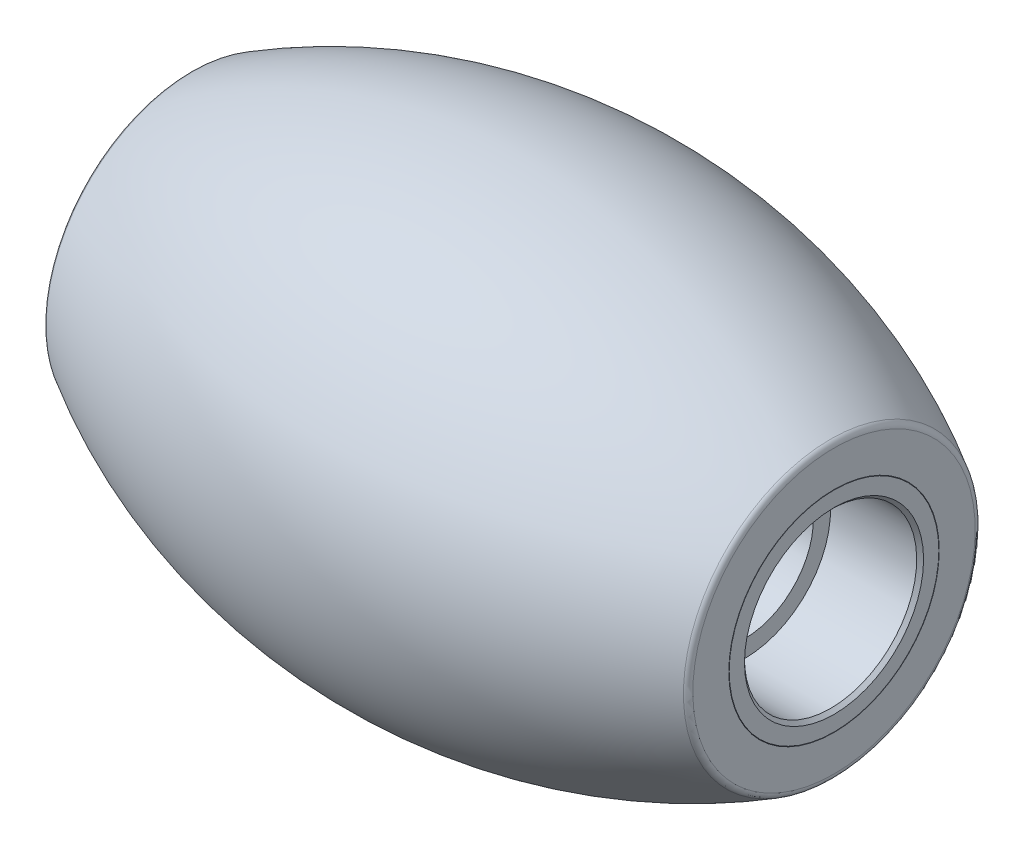
SolidWorks part; units mm, degrees
ref_plane "Face" through (0, 0, 0) normal (0, 0, 1) x (1, 0, 0)
ref_plane "Dessus" through (0, 0, 0) normal (0, 1, 0) x (1, 0, 0)
ref_plane "Droite" through (0, 0, 0) normal (1, 0, 0) x (0, 0, -1)
sketch "Esquisse1" plane through (0, 0, 0) normal (0, 0, 1) x (1, 0, 0)
  line L0 (-9.35, 0) -> (9.35, 0) construction
  line L1 (9.35, 0) -> (9.35, 3.0428)
  line L2 (-9.35, 3.0428) -> (-9.35, 0)
  line L3 (0, 0) -> (0, 5.75) construction
  line L4 (-9.35, 0) -> (9.35, 0)
  arc A0 (-9.35, 3.0428) -> (9.35, 3.0428) centre (0, -11.75) cw
  dimension "D1" = 11.5
  dimension "D3" = 17.5
  dimension "D2" = 18.7
revolve "Révolution1" add sketch "Esquisse1" angle 360 about L4
sketch "Esquisse2" plane through (0, 0, 0) normal (0, 0, 1) x (1, 0, 0)
  line L0 (-9.35, 2.5) -> (-6.75, 2.5)
  line L1 (-9.35, 3.0428) -> (-9.35, -3.0428) construction
  line L2 (-6.75, 2.5) -> (-6.75, 2)
  line L3 (-6.75, 2) -> (6.75, 2)
  line L4 (6.75, 2) -> (6.75, 2.5)
  line L5 (6.75, 2.5) -> (9.35, 2.5)
  line L6 (9.35, -3.0428) -> (9.35, 3.0428) construction
  line L7 (-9.35, 0) -> (9.35, 0) construction
  line L8 (-9.35, 2.5) -> (-9.35, 0)
  line L9 (9.35, 2.5) -> (9.35, 0)
  line L10 (-9.35, 0) -> (9.35, 0)
  dimension "D1" = 5
  dimension "D2" = 2.6
  dimension "D3" = 4
revolve "Enlèvement de matière-Révolution1" cut sketch "Esquisse2" angle 360 about L7
chamfer "Chanfrein1" distance 0.1 angle 45 2 edges at (-9.35, -2.5, 0) (9.35, -2.5, 0)
sketch "Esquisse4" plane through (0, 0, 0) normal (0, 0, 1) x (1, 0, 0)
  line L0 (-9.35, 3.0546) -> (-9.35, 4.2133)
  line L1 (9.35, 3.0546) -> (9.35, 4.2133)
  line L2 (-9.35, 0) -> (9.35, 0) construction
  line L3 (-9.35, 2.6) -> (-9.35, -2.6) construction
  line L4 (9.35, -2.6) -> (9.35, 2.6) construction
  arc A0 (9.35, 3.0428) -> (-9.35, 3.0428) centre (0, -11.75) ccw
  arc A1 (-9.35, -3.0428) -> (9.35, -3.0428) centre (0, 11.75) ccw
  arc A2 (-9.35, -3.0428) -> (9.35, -3.0428) centre (0, 11.75) ccw construction
  arc A3 (9.35, 3.0428) -> (-9.35, 3.0428) centre (0, -11.75) ccw construction
  arc A4 (9.35, 4.2133) -> (-9.35, 4.2133) centre (0, -11.75) ccw
  arc A5 (9.35, 3.0546) -> (-9.35, 3.0546) centre (0, -11.75) ccw
  arc A7 (9.3553, 3.0513) -> (-9.3553, 3.0513) centre (0, -11.75) ccw construction
  arc A8 (9.8843, 3.8881) -> (-9.8843, 3.8881) centre (0, -11.75) ccw construction
  dimension "D3" = 18.5
  dimension "D1" = 1
  dimension "D2" = 0.01
revolve "Révolution2" add sketch "Esquisse4" angle 360 about L2
fillet "Congé1" radius 0.2 2 edges at (-9.35, -4.2133, 0) (9.35, -4.2133, 0)
